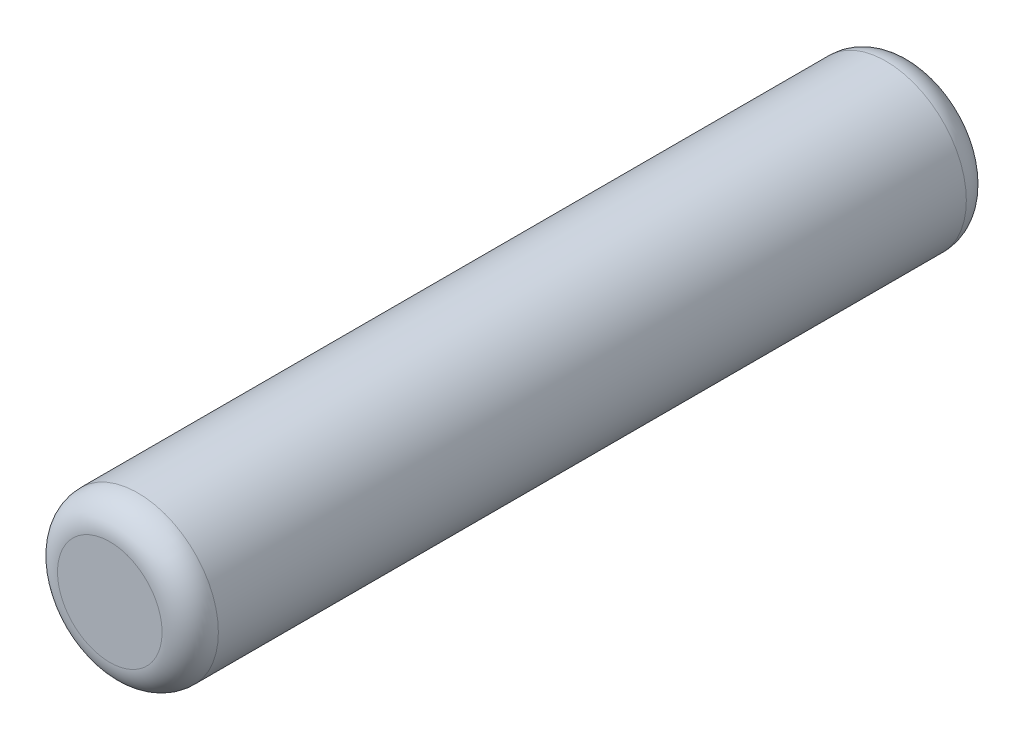
SolidWorks part; units mm, degrees
ref_plane "Front" through (0, 0, 0) normal (0, 0, 1) x (1, 0, 0)
ref_plane "Top" through (0, 0, 0) normal (0, 1, 0) x (1, 0, 0)
ref_plane "Right" through (0, 0, 0) normal (1, 0, 0) x (0, 0, -1)
sketch "Sketch1" plane through (0, 0, 0) normal (0, 0, 1) x (1, 0, 0)
  circle A0 centre (0, 0) radius 1
  dimension "D1" = 2
extrude "Boss-Extrude1" add sketch "Sketch1" along normal mid plane 10
fillet "Fillet1" radius 0.35 2 edges at (1, 0, -5) (1, 0, 5)
